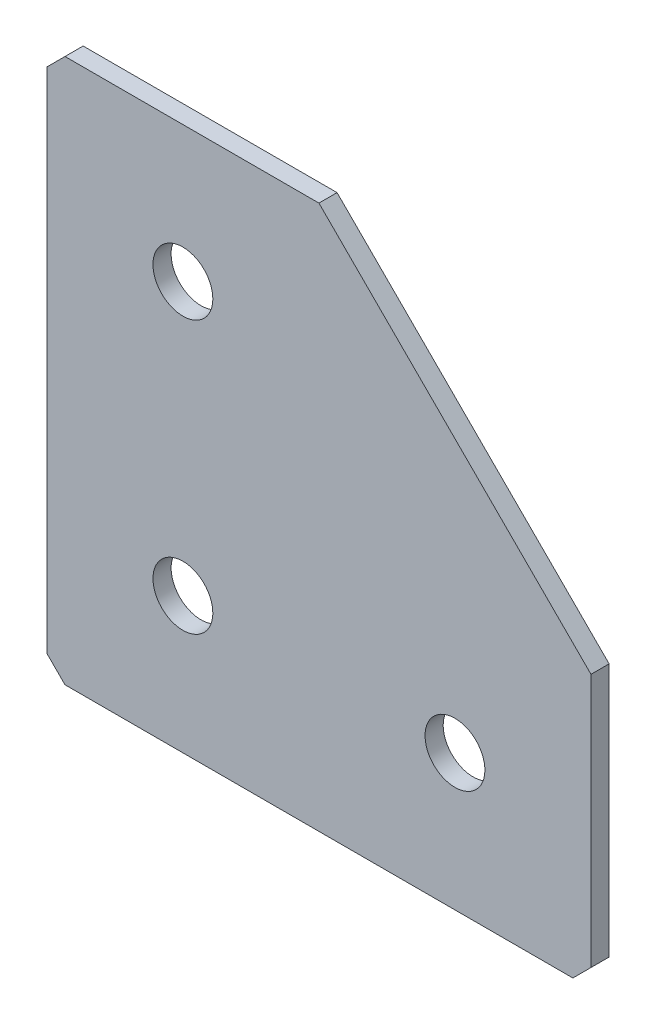
SolidWorks part; units mm, degrees
material "Простая углеродистая сталь"
ref_plane "Спереди(Плоскость XY)" through (0, 0, 0) normal (0, 0, 1) x (1, 0, 0)
ref_plane "Сверху(Плоскость XZ)" through (0, 0, 0) normal (0, 1, 0) x (1, 0, 0)
ref_plane "Справа(Плоскость ZY)" through (0, 0, 0) normal (1, 0, 0) x (0, 0, -1)
sketch "Эскиз1" plane through (0, 0, 0) normal (0, 0, -1) x (1, 0, 0)
  line L0 (0, 0) -> (0, 60)
  line L1 (0, 60) -> (60, 60)
  line L2 (60, 60) -> (60, 30)
  line L3 (60, 30) -> (30, 30) construction
  line L4 (30, 30) -> (30, 0) construction
  line L5 (30, 0) -> (0, 0)
  line L6 (60, 30) -> (30, 0)
  dimension "D1" = 60
  dimension "D2" = 30
  dimension "D3" = 30
  dimension "D4" = 30
extrude "Бобышка-Вытянуть1" add sketch "Эскиз1" along normal blind 2
hole_wizard "Отверстие с зазором M61" positions "Эскиз2" profile "Эскиз3" hole size "M6" standard "DIN" end condition through all
sketch "Эскиз2" plane through (0, 0, -2) normal (0, 0, -1) x (1, 0, 0)
  line L1 (0, 0) -> (30, 0) construction
  line L6 (0, 60) -> (0, 0) construction
  point P4 (15, 45)
  point P6 (15, 15)
  point P29 (45, 45)
  dimension "D1" = 30
  dimension "D2" = 30
  dimension "D4" = 15
  dimension "D5" = 15
sketch "Эскиз3" plane through (15, -45, -2) normal (1, 0, 0) x (0, 1, 0)
  line L0 (0, 0) -> (0, 2)
  line L1 (0, 2) -> (3.3, 2)
  line L2 (3.3, 2) -> (3.3, 0)
  line L5 (3.3, 0) -> (0, 0)
  line L11 (0, -6.35) -> (0, 107.95) construction
  dimension "Диаметр сквозного отверстия" = 6.6
  dimension "Глубина сквозного отверстия" = 2
chamfer "Фаска1" distance 2 angle 45 3 edges at (0, 0, -1) (60, -60, -1) (0, -60, -1)
